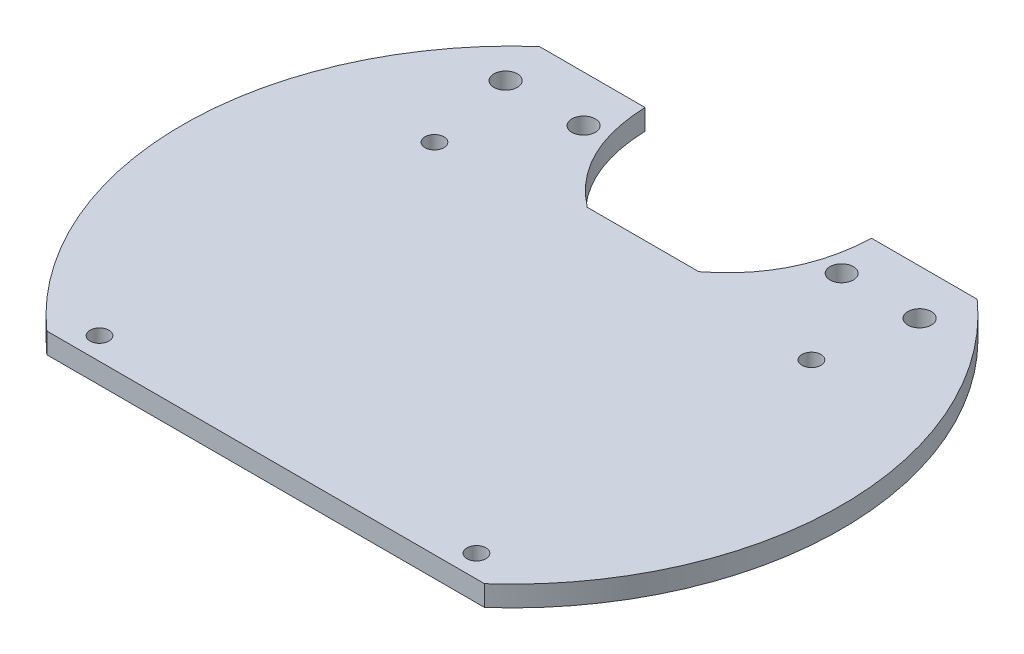
SolidWorks part; units mm, degrees
ref_plane "Front Plane" through (0, 0, 0) normal (0, 0, 1) x (1, 0, 0)
ref_plane "Top Plane" through (0, 0, 0) normal (0, 1, 0) x (1, 0, 0)
ref_plane "Right Plane" through (0, 0, 0) normal (1, 0, 0) x (0, 0, -1)
sketch "Sketch1" plane through (0, 0, 0) normal (0, 1, 0) x (1, 0, 0)
  circle A0 centre (0, 0) radius 50.8
extrude "Boss-Extrude1" add sketch "Sketch1" along normal blind 3.175
sketch "Sketch2" plane through (0, 3.175, 0) normal (0, 1, 0) x (1, 0, 0)
  line L0 (-50.8, 0) -> (50.8, 0) construction
  line L1 (-53.1411, 55.7151) -> (61.7467, 55.7151)
  line L2 (-53.1411, 55.7151) -> (-53.1411, 37.9781)
  line L3 (-53.1411, 37.9781) -> (-17.4664, 37.9781)
  line L4 (61.7467, 55.7151) -> (61.7467, 37.9781)
  line L5 (61.7467, -55.7151) -> (61.7467, -37.9781)
  line L6 (-53.1411, -37.9781) -> (61.7467, -37.9781)
  line L7 (-53.1411, -55.7151) -> (-53.1411, -37.9781)
  line L8 (-53.1411, -55.7151) -> (61.7467, -55.7151)
  line L9 (17.4664, 37.9781) -> (61.7467, 37.9781)
  line L10 (-36.7704, 37.9781) -> (-36.7704, 36.5923) construction
  line L11 (-17.4664, 37.9781) -> (-17.4664, 20.1981) construction
  line L12 (-17.4664, 20.1981) -> (17.4664, 20.1981) construction
  line L13 (17.4664, 37.9781) -> (17.4664, 20.1981) construction
  line L14 (0, 50.8) -> (0, 0) construction
  line L15 (36.7704, 37.9781) -> (36.7704, 36.5923) construction
  line L16 (0, 37.9781) -> (0, 20.1981) construction
  line L17 (-12.7, 37.9781) -> (12.7, 37.9781) construction
  line L18 (-12.7, 37.9781) -> (-12.7, 20.1981) construction
  line L19 (-12.7, 20.1981) -> (12.7, 20.1981) construction
  line L20 (12.7, 37.9781) -> (12.7, 20.1981) construction
  line L21 (0, 25.2781) -> (0, 20.1981) construction
  line L22 (-7.9756, 20.1981) -> (7.9756, 20.1981) construction
  line L26 (-8.5971, 20.1981) -> (8.5971, 20.1981)
  circle A0 centre (0, 0) radius 50.8 construction
  spline S0 degree 2 poles (-17.4664, 37.9781) (-17.0381, 26.7143) (-8.5971, 20.1981) knots 0 0 0 1 1 1
  spline S1 degree 2 poles (17.4664, 37.9781) (17.0381, 26.7143) (8.5971, 20.1981) knots 0 0 0 1 1 1
  point P30 (-98.5223, 46.9213)
  dimension "D1" = 19.304
  dimension "D3" = 17.78
  dimension "D4" = 25.4
  dimension "D5" = 0
  dimension "D8" = 0
extrude "Cut-Extrude1" cut sketch "Sketch2" against normal blind 3.175
sketch "Sketch4" plane through (0, 3.175, 0) normal (0, 1, 0) x (1, 0, 0)
  line L0 (0, 20.1981) -> (0, -37.9781) construction
  line L1 (-8.5971, 20.1981) -> (8.5971, 20.1981) construction
  line L2 (33.7388, -37.9781) -> (-33.7388, -37.9781) construction
sketch "Sketch5" plane through (0, 0, 0) normal (0, -1, 0) x (1, 0, 0)
  line L0 (50.8, 0) -> (-52.1123, 0) construction
  arc A0 (33.7388, -37.9781) -> (33.7388, 37.9781) centre (0, 0) ccw construction
sketch "Sketch6" plane through (0, 3.175, 0) normal (0, 1, 0) x (1, 0, 0)
  circle A0 centre (-29.0576, 17.1018) radius 1.4605
  circle A1 centre (29.0576, 17.1018) radius 1.4605
  circle A2 centre (29.0576, -34.5364) radius 1.4605
  circle A3 centre (-29.0576, -34.5364) radius 1.4605
extrude "Cut-Extrude2" cut sketch "Sketch6" against normal blind 3.175
sketch "Sketch7" plane through (0, 0, 0) normal (0, -1, 0) x (1, 0, 0)
  circle A0 centre (29.3256, 19.3504) radius 1.3462
  circle A1 centre (42.5336, 19.3504) radius 1.3462
  circle A2 centre (44.1338, -11.8281) radius 1.3462
  circle A3 centre (27.7254, -11.8281) radius 1.3462
sketch "Sketch8" plane through (0, 0, 0) normal (0, -1, 0) x (1, 0, 0)
  circle A0 centre (-31.7996, -30.8198) radius 1.8116
  circle A1 centre (-19.7854, -30.8198) radius 1.8093
  circle A2 centre (19.8309, -30.9939) radius 1.7977
  circle A3 centre (31.8451, -30.9939) radius 1.8156
extrude "Cut-Extrude4" cut sketch "Sketch8" against normal blind 3.175
